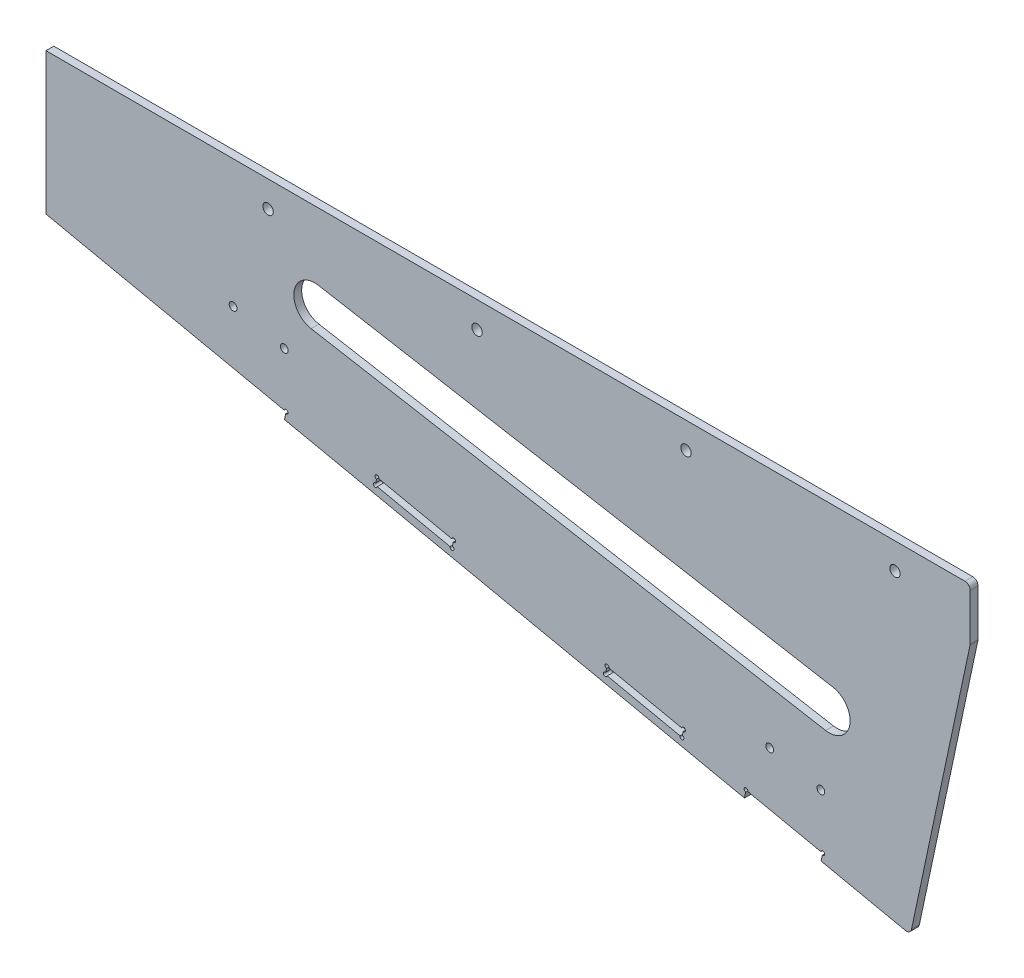
SolidWorks part; units mm, degrees
ref_plane "前视基准面" through (0, 0, 0) normal (0, 0, 1) x (1, 0, 0)
ref_plane "上视基准面" through (0, 0, 0) normal (0, 1, 0) x (1, 0, 0)
ref_plane "右视基准面" through (0, 0, 0) normal (1, 0, 0) x (0, 0, -1)
sketch "草图1" plane through (0, 0, 0) normal (0, 0, 1) x (1, 0, 0)
  line L0 (-31.7701, 71.7677) -> (318.2299, 71.7677)
  line L1 (318.2299, 71.7677) -> (292.9319, -47.2498)
  line L2 (292.9319, -47.2498) -> (-31.7701, 21.7677)
  line L3 (-31.7701, 21.7677) -> (-31.7701, 71.7677)
  dimension "D1" = 78
  dimension "D2" = 350
  dimension "D3" = 50
extrude "凸台-拉伸1" add sketch "草图1" along normal blind 3
sketch "草图3" plane through (0, 0, 3) normal (0, 0, 1) x (1, 0, 0)
  line L0 (-0.4694, 15.1145) -> (0.1544, 18.049)
  line L1 (-31.7701, 21.7677) -> (292.9319, -47.2498) construction
  line L2 (0.1544, 18.049) -> (-31.7701, 24.8347)
  line L3 (-31.7701, 71.7677) -> (-31.7701, 21.7677) construction
  line L4 (-31.7701, 24.8347) -> (-31.7701, 21.7677)
  line L5 (-31.7701, 21.7677) -> (-0.4694, 15.1145)
  line L7 (242.6174, -36.5552) -> (240.1118, -45.9064) construction
  line L8 (240.1118, -45.9064) -> (269.0895, -53.671) construction
  line L9 (269.0895, -53.671) -> (271.5952, -44.3197) construction
  line L10 (271.5952, -44.3197) -> (242.6174, -36.5552) construction
  line L12 (176.2209, -19.3751) -> (205.5654, -25.6125)
  line L13 (175.5972, -22.3096) -> (176.2209, -19.3751)
  line L14 (204.9416, -28.5469) -> (175.5972, -22.3096)
  line L15 (205.5654, -25.6125) -> (204.9416, -28.5469)
  dimension "D2" = 180
  dimension "D3" = 30
  dimension "D1" = 3
  dimension "D4" = 3
  dimension "D5" = 32
extrude "切除-拉伸2" cut sketch "草图3" against normal blind 10
sketch "草图7" plane through (0, 0, 3) normal (0, 0, 1) x (1, 0, 0)
  line L0 (292.9319, -47.2498) -> (239.1338, -35.8147)
  line L1 (204.9416, -28.5469) -> (292.9319, -47.2498) construction
  line L2 (239.1338, -35.8147) -> (262.0012, 71.7677)
  line L3 (318.2299, 71.7677) -> (-31.7701, 71.7677) construction
  line L4 (262.0012, 71.7677) -> (318.2299, 71.7677)
  line L5 (318.2299, 71.7677) -> (292.9319, -47.2498)
  dimension "D1" = 55
extrude "切除-拉伸6" cut sketch "草图7" against normal through all
sketch "草图8" plane through (0, 0, 3) normal (0, 0, 1) x (1, 0, 0)
  circle A0 centre (182.503, -9.7647) radius 1.5
  circle A1 centre (201.8215, -14.9411) radius 1.5
  dimension "D1" = 3
  dimension "D2" = 3
extrude "切除-拉伸7" [suppressed] cut sketch "草图8" against normal through all
sketch "草图12" plane through (0, 0, 3) normal (0, 0, 1) x (1, 0, 0)
  line L0 (-31.7701, 71.7677) -> (-31.7701, 91.7677)
  line L1 (-31.7701, 91.7677) -> (262.0012, 91.7677)
  line L2 (262.0012, 91.7677) -> (262.0012, 71.7677)
  line L3 (262.0012, 71.7677) -> (-31.7701, 71.7677)
  dimension "D1" = 90
  dimension "D2" = 20
extrude "凸台-拉伸2" add sketch "草图12" against normal blind 3
sketch "草图13" plane through (0, 0, 3) normal (0, 0, 1) x (1, 0, 0)
  line L0 (262.0012, 91.7677) -> (-31.7701, 91.7677) construction
  line L1 (-31.7701, 91.7677) -> (-31.7701, 24.8347) construction
  circle A0 centre (-6.7701, 81.7677) radius 2
  circle A1 centre (73.2299, 81.7677) radius 2
  circle A2 centre (153.2299, 81.7677) radius 2
  circle A3 centre (233.2299, 81.7677) radius 2
  dimension "D1" = 80
  dimension "D2" = 80
  dimension "D3" = 80
  dimension "D4" = 4
  dimension "D5" = 10
  dimension "D6" = 10
  dimension "D7" = 10
  dimension "D8" = 10
  dimension "D9" = 25
  dimension "D10" = 4
  dimension "D11" = 4
  dimension "D12" = 4
extrude "切除-拉伸9" cut sketch "草图13" against normal through all
sketch "草图14" plane through (0, 0, 3) normal (0, 0, 1) x (1, 0, 0)
  line L0 (11.0933, 58.2375) -> (208.0548, 23.5079) construction
  line L1 (12.4825, 66.1159) -> (209.444, 31.3863)
  line L2 (9.7041, 50.359) -> (206.6657, 15.6294)
  arc A0 (12.4825, 66.1159) -> (9.7041, 50.359) centre (11.0933, 58.2375) ccw
  arc A1 (206.6657, 15.6294) -> (209.444, 31.3863) centre (208.0548, 23.5079) ccw
  point P2 (109.5741, 40.8727)
  dimension "D1" = 200
extrude "切除-拉伸10" cut sketch "草图14" against normal blind 10
hole_wizard "大小mm 暗销槽口2" positions "草图16" profile "草图17" size "Ø1.5" standard "GB" slot yes end condition through all
sketch "草图16" plane through (0, 0, 3) normal (0, 0, 1) x (1, 0, 0)
  point P0 (0.1544, 18.049)
  point P3 (176.2209, -19.3751)
  point P6 (205.5654, -25.6125)
sketch "草图17" plane through (0.1544, 18.049, 3) normal (1, 0, 0) x (0, -1, 0)
  line L0 (0, 0) -> (0, 3)
  line L1 (0, 3) -> (0.75, 3)
  line L2 (0.75, 3) -> (0.75, 0)
  line L5 (0.75, 0) -> (0, 0)
  line L11 (0, -6.35) -> (0, 107.95) construction
  dimension "通孔孔直径" = 1.5
  dimension "通孔孔深度" = 3
sketch "草图18" plane through (0, 0, 0) normal (0, 0, -1) x (-1, 0, 0)
  line L0 (-152.2916, -11.2218) -> (-151.6679, -14.1562)
  line L1 (-151.6679, -14.1562) -> (-122.3235, -7.9189)
  line L2 (-122.3235, -7.9189) -> (-122.9472, -4.9844)
  line L3 (-122.9472, -4.9844) -> (-152.2916, -11.2218)
  line L4 (-64.2584, 7.4903) -> (-63.6346, 4.5558)
  line L5 (-63.6346, 4.5558) -> (-34.2902, 10.7932)
  line L6 (-34.2902, 10.7932) -> (-34.9139, 13.7276)
  line L7 (-34.9139, 13.7276) -> (-64.2584, 7.4903)
extrude "切除-拉伸11" cut sketch "草图18" against normal through all
hole_wizard "大小mm 暗销槽口3" positions "草图19" profile "草图20" size "Ø1.5" standard "GB" slot yes end condition through all
sketch "草图19" plane through (0, 0, 0) normal (0, 0, -1) x (-1, 0, 0)
  line L0 (-151.6679, -14.1562) -> (-122.3235, -7.9189) construction
  line L1 (-152.2916, -11.2218) -> (-151.6679, -14.1562) construction
  point P0 (-152.2916, -11.2218)
  point P3 (-151.6679, -14.1562)
  point P9 (-122.3235, -7.9189)
  point P12 (-122.9472, -4.9844)
  point P15 (-64.2584, 7.4903)
  point P18 (-63.6346, 4.5558)
  point P21 (-34.2902, 10.7932)
  point P24 (-34.9139, 13.7276)
sketch "草图20" plane through (152.2916, -11.2218, 0) normal (1, 0, 0) x (0, 1, 0)
  line L0 (0, 0) -> (0, 3)
  line L1 (0, 3) -> (0.75, 3)
  line L2 (0.75, 3) -> (0.75, 0)
  line L5 (0.75, 0) -> (0, 0)
  line L11 (0, -6.35) -> (0, 107.95) construction
  dimension "通孔孔直径" = 1.5
  dimension "通孔孔深度" = 3
fillet "圆角1" radius 2 5 edges at (-31.7701, 91.7677, 1.5) (-31.7701, 24.8347, 1.5) (239.1338, -35.8147, 1.5) (262.0012, 71.7677, 1.5) (262.0012, 91.7677, 1.5)
sketch "草图21" plane through (0, 0, 3) normal (0, 0, 1) x (1, 0, 0)
  line L0 (-91.7701, 37.5881) -> (-13.8624, 21.0283)
  line L2 (-13.8624, 91.7677) -> (-81.3829, 91.7677)
  line L3 (260.0012, 91.7677) -> (-29.7701, 91.7677) construction
  line L4 (-91.7701, 91.7677) -> (-91.7701, 37.5881)
  line L7 (-81.3829, 91.7677) -> (-91.7701, 91.7677)
  line L8 (-13.8624, 91.7677) -> (-13.8624, 21.0283)
extrude "凸台-拉伸3" add sketch "草图21" against normal blind 3
sketch "草图4" plane through (0, 0, 3) normal (0, 0, 1) x (1, 0, 0)
  circle A4 centre (-20.1411, 42.8097) radius 1.5
  circle A5 centre (-0.5781, 38.6515) radius 1.5
  circle A6 centre (185.2699, -0.8517) radius 1.5
  circle A7 centre (204.8328, -5.01) radius 1.5
  dimension "D1" = 3
  dimension "D2" = 3
  dimension "D3" = 3
  dimension "D4" = 3
extrude "切除-拉伸3" cut sketch "草图4" against normal blind 10
